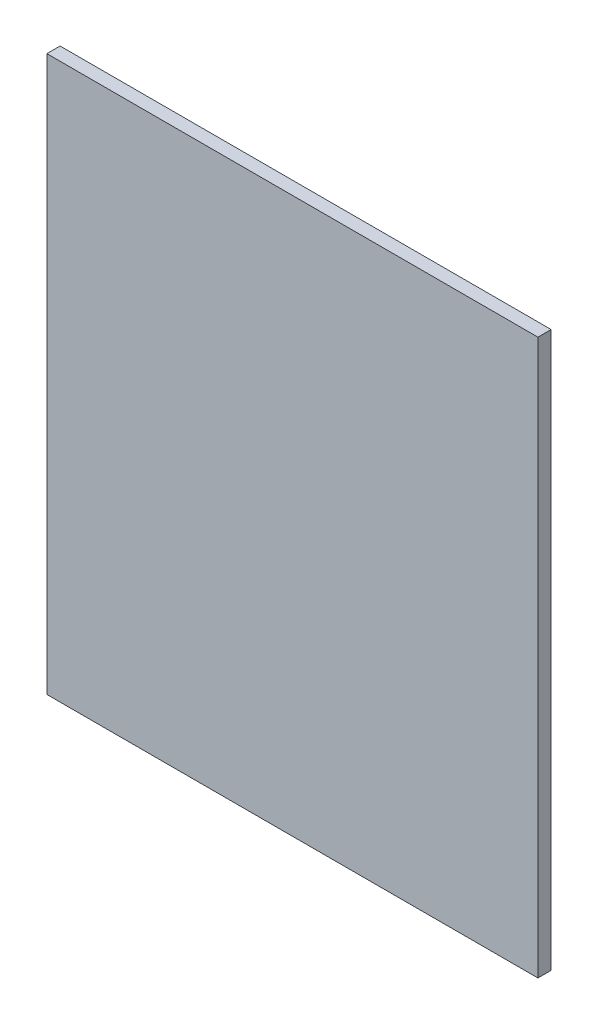
SolidWorks part; units mm, degrees
ref_plane "Front Plane" through (0, 0, 0) normal (0, 0, 1) x (1, 0, 0)
ref_plane "Top Plane" through (0, 0, 0) normal (0, 1, 0) x (1, 0, 0)
ref_plane "Right Plane" through (0, 0, 0) normal (1, 0, 0) x (0, 0, -1)
sketch "Sketch4" plane through (0, 0, 0) normal (0, 0, 1) x (1, 0, 0)
  line L0 (-235.9576, 266.6736) -> (-235.9576, 0)
  line L1 (-235.9576, 0) -> (0, 0)
  line L2 (0, 0) -> (0, 266.6736)
  line L3 (0, 266.6736) -> (-235.9576, 266.6736)
  line L4 (-181.63, 126.6736) -> (-235.9576, 126.6736) construction
  dimension "D6" = 140
  dimension "D7" = 266.6736
  dimension "D8" = 235.9576
  dimension "D10" = 266.6736
  dimension "D11" = 235.9576
extrude "Boss-Extrude1" add sketch "Sketch4" along normal mid plane 6.35
scale "Scale1" scale about origin uniform scaling yes scale factor 0.8
